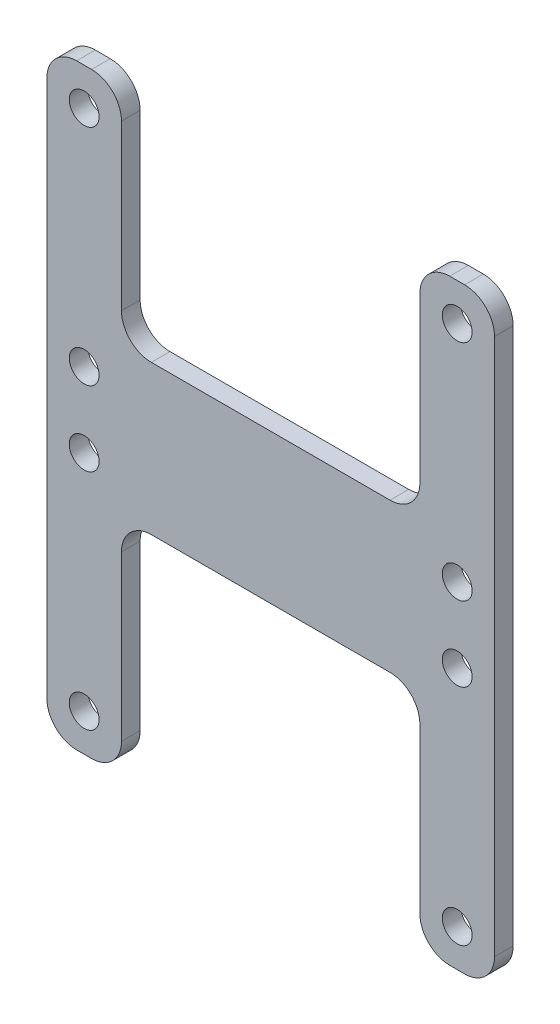
SolidWorks part; units mm, degrees
material "ABS"
ref_plane "Front Plane" through (0, 0, 0) normal (0, 0, 1) x (1, 0, 0)
ref_plane "Top Plane" through (0, 0, 0) normal (0, 1, 0) x (1, 0, 0)
ref_plane "Right Plane" through (0, 0, 0) normal (1, 0, 0) x (0, 0, -1)
sketch "Sketch1" plane through (0, 0, 0) normal (0, 0, 1) x (1, 0, 0)
  line L0 (-38.1, 0) -> (38.1, 0)
  line L1 (-38.1, 50.8) -> (-25.4, 50.8)
  line L2 (-38.1, 50.8) -> (-38.1, -50.8)
  line L3 (-38.1, -50.8) -> (-25.4, -50.8)
  line L4 (38.1, 50.8) -> (38.1, -50.8)
  line L5 (-38.1, 50.8) -> (38.1, -50.8) construction
  line L6 (-38.1, -50.8) -> (38.1, 50.8) construction
  line L7 (-25.4, 50.8) -> (-25.4, 12.7)
  line L8 (-25.4, 12.7) -> (25.4, 12.7)
  line L9 (25.4, 12.7) -> (25.4, 50.8)
  line L10 (25.4, 50.8) -> (38.1, 50.8)
  line L11 (25.4, 12.7) -> (25.4, 0) construction
  line L12 (-25.4, -50.8) -> (-25.4, -12.7)
  line L13 (-25.4, -12.7) -> (25.4, -12.7)
  line L14 (25.4, -12.7) -> (25.4, -50.8)
  line L15 (25.4, -50.8) -> (38.1, -50.8)
  point P0 (0, 0)
  dimension "D1" = 76.2
  dimension "D2" = 101.6
  dimension "D3" = 12.7
extrude "Boss-Extrude1" add sketch "Sketch1" along normal blind 3.175 contours L4 L1 L2 L0 | L4 L0 L2 L3
sketch "Sketch4" plane through (0, 0, 3.175) normal (0, 0, 1) x (1, 0, 0)
  line L0 (-31.75, 44.45) -> (-31.75, 6.35) construction
  line L1 (-31.75, 6.35) -> (31.75, 6.35) construction
  line L2 (31.75, 6.35) -> (31.75, 44.45) construction
  line L3 (31.75, 44.45) -> (-31.75, 44.45) construction
  line L4 (31.75, 44.45) -> (31.75, 50.8) construction
  line L5 (25.4, 50.8) -> (38.1, 50.8) construction
  line L6 (0, 6.35) -> (0, 0) construction
  line L7 (-38.1, 0) -> (38.1, 0) construction
  line L8 (-38.1, 50.8) -> (-38.1, -50.8) construction
  line L9 (38.1, 50.8) -> (38.1, -50.8) construction
  circle A0 centre (-31.75, 44.45) radius 2.54
  circle A1 centre (-31.75, 6.35) radius 2.54
  circle A2 centre (31.75, 6.35) radius 2.54
  circle A3 centre (31.75, 44.45) radius 2.54
  circle A4 centre (-31.75, -6.35) radius 2.54
  circle A5 centre (31.75, -6.35) radius 2.54
  circle A6 centre (31.75, -44.45) radius 2.54
  circle A7 centre (-31.75, -44.45) radius 2.54
  dimension "D1" = 5.08
  dimension "D2" = 63.5
  dimension "D3" = 38.1
extrude "Cut-Extrude3" cut sketch "Sketch4" against normal through all
fillet "Fillet1" radius 5.08 4 edges at (-25.4, -12.7, 1.5875) (25.4, -12.7, 1.5875) (25.4, 12.7, 1.5875) (-25.4, 12.7, 1.5875)
fillet "Fillet2" radius 5.08 8 edges at (38.1, -50.8, 1.5875) (25.4, -50.8, 1.5875) (-25.4, -50.8, 1.5875) (-38.1, -50.8, 1.5875) (-38.1, 50.8, 1.5875) (-25.4, 50.8, 1.5875) (25.4, 50.8, 1.5875) (38.1, 50.8, 1.5875)
